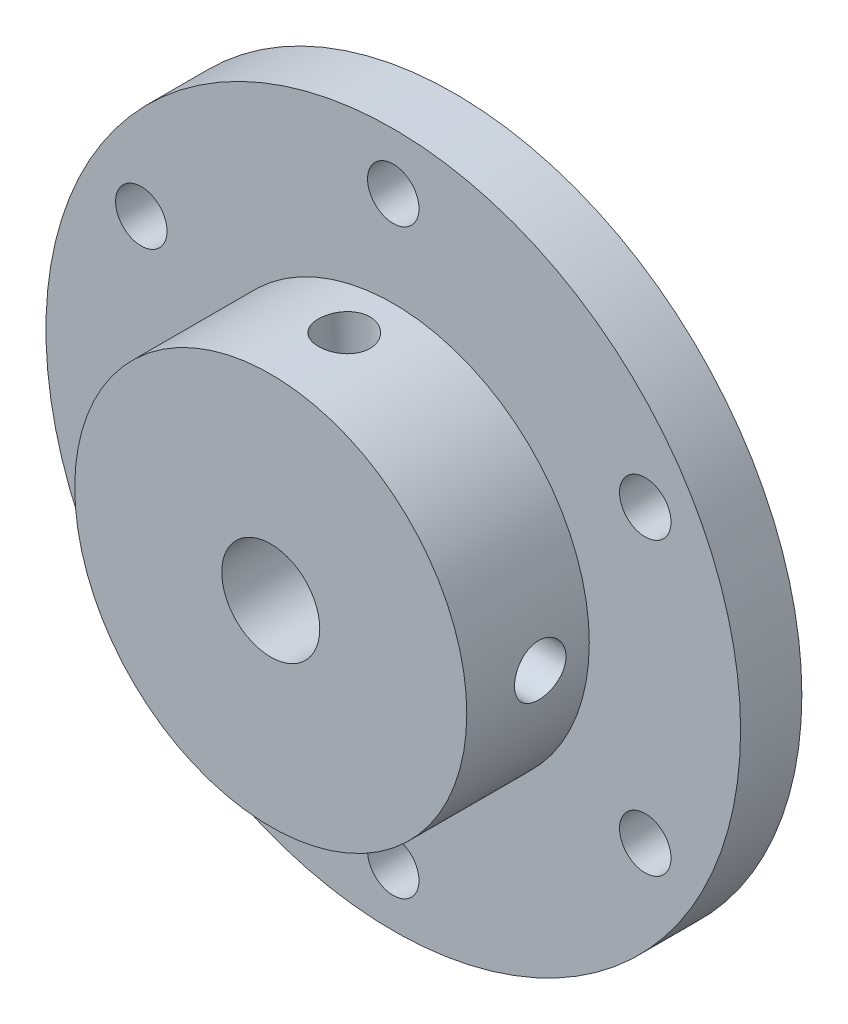
SolidWorks part; units mm, degrees
material "6061 合金"
ref_plane "前基準面" through (0, 0, 0) normal (0, 0, 1) x (1, 0, 0)
ref_plane "上基準面" through (0, 0, 0) normal (0, 1, 0) x (1, 0, 0)
ref_plane "右基準面" through (0, 0, 0) normal (1, 0, 0) x (0, 0, -1)
sketch "草圖1" plane through (0, 0, 0) normal (0, 0, 1) x (1, 0, 0)
  circle A0 centre (0, 0) radius 28.35
  dimension "D1" = 56.7
extrude "填料-伸長1" add sketch "草圖1" along normal blind 5
sketch "草圖2" plane through (0, 0, 5) normal (0, 0, 1) x (1, 0, 0)
  circle A0 centre (0, 0) radius 16
  dimension "D1" = 32
extrude "填料-伸長2" add sketch "草圖2" along normal blind 10
sketch "草圖3" plane through (0, 0, 15) normal (0, 0, 1) x (1, 0, 0)
  circle A0 centre (0, 0) radius 4
  dimension "D1" = 8
extrude "除料-伸長1" cut sketch "草圖3" against normal through all
sketch "草圖4" plane through (0, 0, 5) normal (0, 0, 1) x (1, 0, 0)
  line L0 (0, 0) -> (0, 23.75) construction
  circle A0 centre (0, 23.75) radius 2.6
  dimension "D2" = 5.2
  dimension "D1" = 23.75
ref_plane "平面1" through (16, 0, 0) normal (1, 0, 0) x (0, 0, -1)
hole_wizard "M5x0.8 螺紋孔1" positions "3D草圖1" profile "草圖8" tap size "M5x0.8" standard "Ansi Metric" end condition through all
sketch3d "3D草圖1"
  point P0 (0, 23.75, 5)
sketch "草圖8" plane through (0, 23.75, 5) normal (1, 0, 0) x (0, -1, 0)
  line L0 (0, 0) -> (0, 5)
  line L1 (0, 5) -> (2.1, 5)
  line L2 (2.1, 5) -> (2.1, 0)
  line L5 (2.1, 0) -> (0, 0)
  line L11 (0, -6.35) -> (0, 107.95) construction
  dimension "砮 脸ふ苝 畖" = 4.2
  dimension "砮 脸ふ苝瞏 " = 5
pattern_circular "環狀複製排列1" count 6 over 360 about axis through (0, 0, 0) along (0, 0, 1) of "M5x0.8 螺紋孔1"
hole_wizard "M5x0.8 螺紋孔2" positions "草圖9" profile "草圖11" tap size "M5x0.8" standard "Ansi Metric"
sketch "草圖9" plane through (0, 0, 0) normal (1, 0, 0) x (0, 0, -1)
  line L4 (-5, 28.35) -> (-5, -28.35) construction
  line L5 (0, 0) -> (-15, 0) construction
  line L6 (-15, 16) -> (-15, -16) construction
  point P0 (-9, 0)
  dimension "D1" = 4
sketch "草圖11" plane through (0, 0, 9) normal (0, 1, 0) x (0, 0, 1)
  line L0 (0, 0) -> (0, 16.001)
  line L1 (0, 16.001) -> (2.1, 16.001)
  line L2 (2.1, 16.001) -> (2.1, 0)
  line L5 (2.1, 0) -> (0, 0)
  line L11 (0, -6.35) -> (0, 107.95) construction
  dimension "貫穿螺孔鑽直徑" = 4.2
  dimension "貫穿螺孔鑽深度" = 16.001
pattern_circular "環狀複製排列2" count 2 every 90 about axis through (0, 0, 15) along (0, 0, -1) of "M5x0.8 螺紋孔2"
